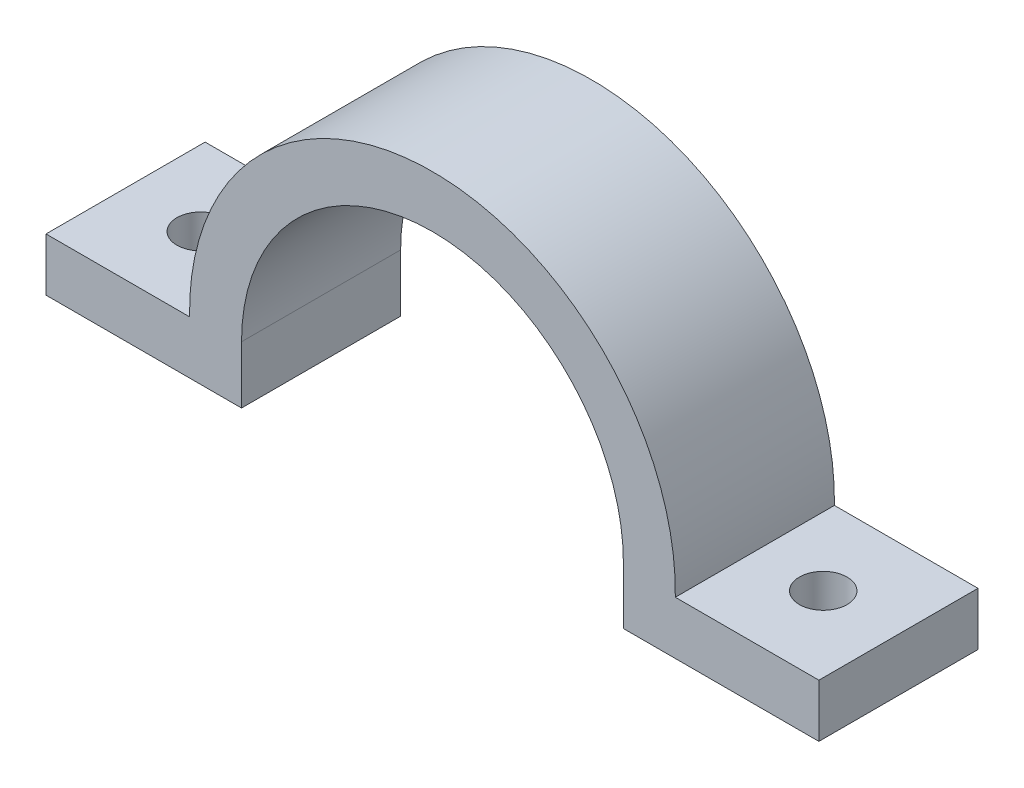
SolidWorks part; units mm, degrees
ref_plane "Front Plane" through (0, 0, 0) normal (0, 0, 1) x (1, 0, 0)
ref_plane "Top Plane" through (0, 0, 0) normal (0, 1, 0) x (1, 0, 0)
ref_plane "Right Plane" through (0, 0, 0) normal (1, 0, 0) x (0, 0, -1)
ref_plane "Plane1" through (0, -7, 0) normal (0, 1, 0) x (1, 0, 0)
sketch "Sketch3" plane through (0, 0, 0) normal (0, 0, 1) x (1, 0, 0)
  line L0 (18, -5.4125) -> (36.4334, -5.4125)
  line L1 (-36.4334, -5.4125) -> (-18, -5.4125)
  line L2 (40.0767, -7) -> (-40.0767, -7) construction
  line L3 (-36.4334, -0.4125) -> (-22.8963, -0.4125)
  line L4 (36.4334, -0.4125) -> (22.8963, -0.4125)
  line L5 (-36.4334, -5.4125) -> (-36.4334, -0.4125)
  line L6 (36.4334, -5.4125) -> (36.4334, -0.4125)
  line L7 (18, -5.4125) -> (18, 0)
  line L8 (-18, -5.4125) -> (-18, 0)
  circle A0 centre (0, 0) radius 18
  circle A1 centre (0, 0) radius 22.9
  dimension "D1" = 45.8
  dimension "D2" = 36
  dimension "D3" = 1.5875
  dimension "D4" = 5
  dimension "D5" = 36.4334
extrude "Boss-Extrude1" add sketch "Sketch3" along normal blind 15 contours A1 L3 L5 L1 | A1 L1 L8 A0 L7 L0 | A1 L0 L6 L4
sketch "Sketch5" plane through (0, -0.4125, 0) normal (0, 1, 0) x (1, 0, 0)
  line L0 (-29.3423, -7.5) -> (29.3423, -7.5) construction
  line L1 (36.4334, -15) -> (36.4334, 0) construction
  circle A0 centre (-29.3423, -7.5) radius 2.25
  circle A1 centre (29.3423, -7.5) radius 2.25
  point P4 (0, -7.5)
  point P8 (36.4334, -7.5)
  point P9 (30.6081, -7.5)
  dimension "D1" = 4.5
  dimension "D2" = 58.6846
extrude "Cut-Extrude1" cut sketch "Sketch5" against normal through all both and the other way through all
